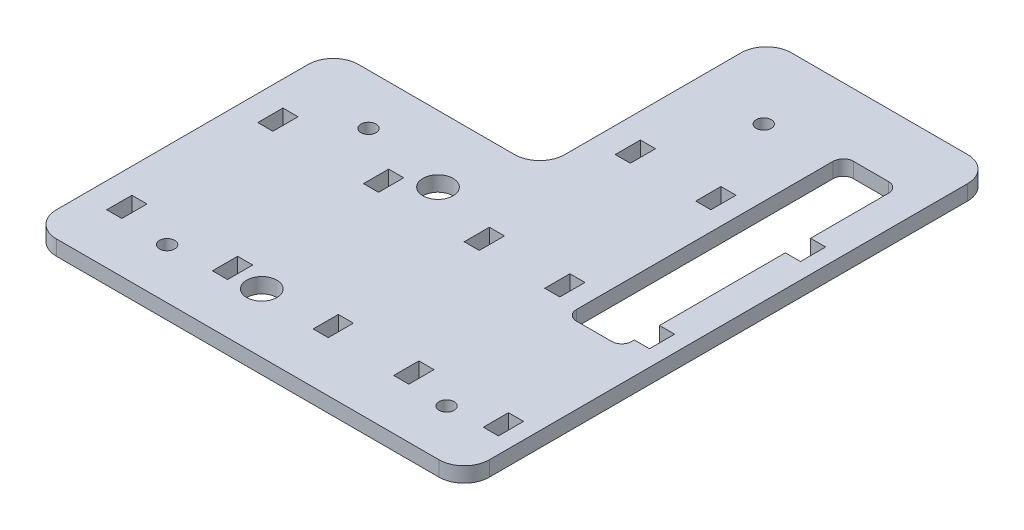
SolidWorks part; units mm, degrees
ref_plane "Front Plane" through (0, 0, 0) normal (0, 0, 1) x (1, 0, 0)
ref_plane "Top Plane" through (0, 0, 0) normal (0, 1, 0) x (1, 0, 0)
ref_plane "Right Plane" through (0, 0, 0) normal (1, 0, 0) x (0, 0, -1)
sketch "Sketch1" plane through (0, 0, 0) normal (0, 1, 0) x (1, 0, 0)
  line L1 (0, 0) -> (86, 0)
  line L2 (0, 0) -> (0, 105)
  line L3 (0, 105) -> (86, 105)
  line L4 (86, 0) -> (86, 105)
  dimension "D1" = 105
  dimension "D2" = 86
extrude "Boss-Extrude1" add sketch "Sketch1" along normal blind 3
ref_plane "Plane6" through (0, 0, -100) normal (0, 0, -1) x (-1, 0, 0)
ref_plane "Plane1" through (0, 0, -52.5) normal (0, 0, 1) x (1, 0, 0)
sketch "Sketch2" plane through (0, 3, 0) normal (0, 1, 0) x (1, 0, 0)
  line L0 (0, 105) -> (0, 0) construction
  line L1 (65, 10) -> (62, 10)
  line L2 (65, 10) -> (65, 15)
  line L3 (65, 15) -> (62, 15)
  line L4 (62, 10) -> (62, 15)
  line L9 (49, 10) -> (46, 10)
  line L10 (49, 10) -> (49, 15)
  line L11 (49, 15) -> (46, 15)
  line L12 (46, 10) -> (46, 15)
  line L13 (29, 10) -> (26, 10)
  line L14 (29, 10) -> (29, 15)
  line L15 (29, 15) -> (26, 15)
  line L16 (26, 10) -> (26, 15)
  line L17 (8, 10) -> (5, 10)
  line L18 (8, 10) -> (8, 15)
  line L19 (8, 15) -> (5, 15)
  line L20 (5, 10) -> (5, 15)
  line L21 (0, 0) -> (86, 0) construction
  line L23 (79.8, 15) -> (82.8, 15)
  line L24 (79.8, 15) -> (79.8, 10)
  line L25 (79.8, 10) -> (82.8, 10)
  line L26 (82.8, 15) -> (82.8, 10)
  dimension "D1" = 3
  dimension "D2" = 13
  dimension "D3" = 3
  dimension "D4" = 3
  dimension "D5" = 3
  dimension "D6" = 3
  dimension "D7" = 14.8
  dimension "D8" = 17
  dimension "D9" = 18
  dimension "D10" = 5
  dimension "D11" = 10
  dimension "D12" = 5
extrude "Cut-Extrude1" cut sketch "Sketch2" against normal blind 3
pattern_linear "LPattern1" count 3 spacing 30 along (0, 0, -1) of "Cut-Extrude1"
sketch "Sketch5" plane through (0, 3, 0) normal (0, 1, 0) x (1, 0, 0)
  line L0 (49, 75) -> (46, 75) construction
  line L1 (65, 15) -> (62, 15) construction
  line L2 (8, 45) -> (5, 45) construction
  line L3 (49, 70) -> (49, 75) construction
  line L4 (65, 10) -> (65, 15) construction
  line L5 (8, 40) -> (8, 45) construction
  circle A0 centre (17, 10) radius 1.5
  circle A1 centre (17, 50) radius 1.5
  circle A2 centre (72.5, 10) radius 1.5
  circle A3 centre (55.5, 90) radius 1.5
  dimension "D1" = 3
  dimension "D2" = 3
  dimension "D3" = 3
  dimension "D4" = 3
  dimension "D5" = 15
  dimension "D6" = 5
  dimension "D7" = 5
  dimension "D8" = 6.5
  dimension "D9" = 7.5
  dimension "D10" = 9
extrude "Cut-Extrude2" cut sketch "Sketch5" against normal through all
sketch "Sketch6" plane through (0, 3, 0) normal (0, 1, 0) x (1, 0, 0)
  line L0 (62, 45) -> (62, 40) construction
  line L1 (79.8, 75) -> (79.8, 70) construction
  line L2 (86, 105) -> (0, 105) construction
  line L3 (68.8, 92.5) -> (79.8, 92.5)
  line L4 (68.8, 92.5) -> (68.8, 37.5)
  line L5 (68.8, 37.5) -> (79.8, 37.5)
  line L6 (79.8, 92.5) -> (79.8, 37.5)
  line L8 (6.7203, 29.3) -> (39.734, 29.3) construction
  line L9 (0, 0) -> (86, 0) construction
  circle A0 centre (34, 11.8) radius 3
  circle A1 centre (34, 46.8) radius 3
  dimension "D3" = 6
  dimension "D4" = 6
  dimension "D1" = 28
  dimension "D2" = 35
  dimension "D5" = 17.5
  dimension "D6" = 11
  dimension "D7" = 55
  dimension "D8" = 12.5
  dimension "D9" = 29.3
extrude "Cut-Extrude3" cut sketch "Sketch6" against normal through all
fillet "Fillet2" radius 2 4 edges at (79.8, 1.5, -37.5) (68.8, 1.5, -37.5) (68.8, 1.5, -92.5) (79.8, 1.5, -92.5)
sketch "Sketch7" plane through (0, 3, 0) normal (0, 1, 0) x (1, 0, 0)
  line L0 (46, 75) -> (46, 70) construction
  line L1 (0, 105) -> (41, 105)
  line L2 (0, 105) -> (0, 60)
  line L3 (0, 60) -> (41, 60)
  line L4 (41, 105) -> (41, 60)
  circle A0 centre (17, 50) radius 1.5 construction
  dimension "D1" = 10
  dimension "D2" = 5
extrude "Cut-Extrude4" cut sketch "Sketch7" against normal through all
fillet "Fillet3" radius 5 6 edges at (86, 1.5, -105) (41, 1.5, -105) (41, 1.5, -60) (0, 1.5, -60) (86, 1.5, 0) (0, 1.5, 0)
